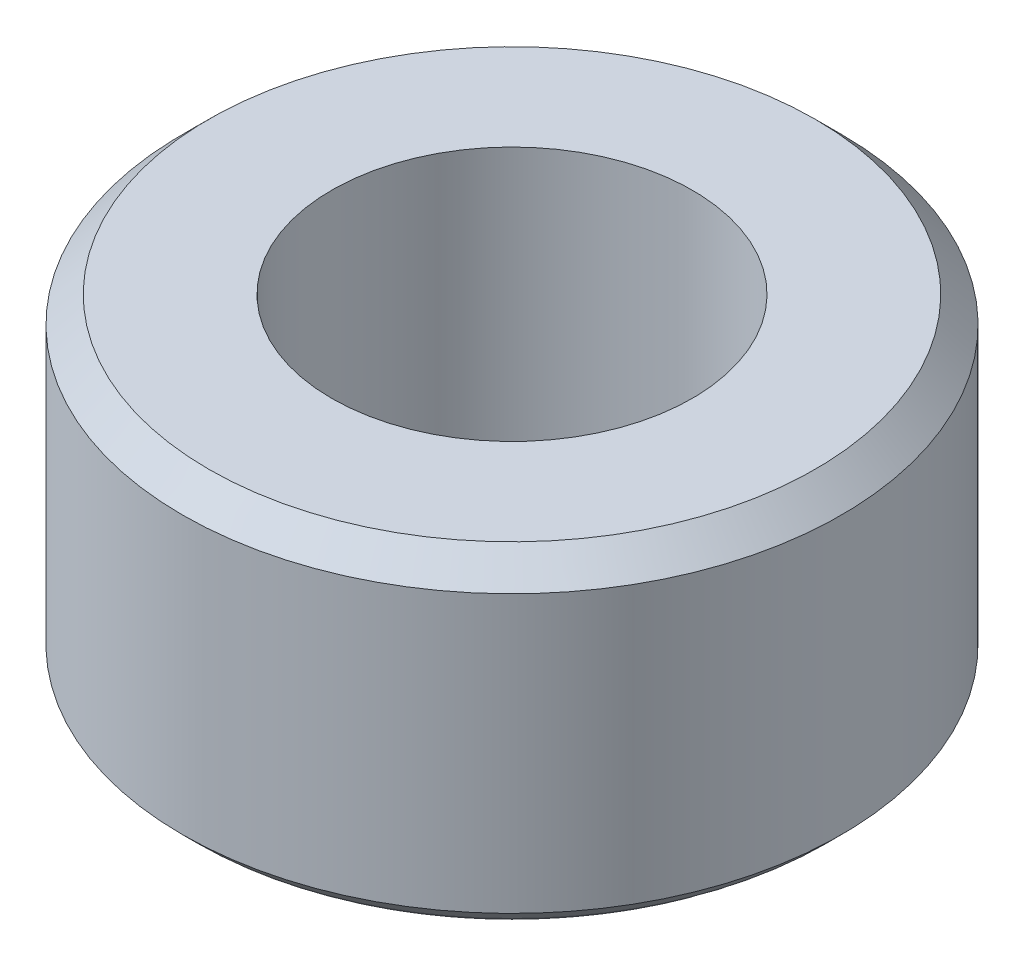
SolidWorks part; units mm, degrees
ref_plane "Front Plane" through (0, 0, 0) normal (0, 0, 1) x (1, 0, 0)
ref_plane "Top Plane" through (0, 0, 0) normal (0, 1, 0) x (1, 0, 0)
ref_plane "Right Plane" through (0, 0, 0) normal (1, 0, 0) x (0, 0, -1)
sketch "Sketch1" plane through (0, 0, 0) normal (0, 1, 0) x (1, 0, 0)
  circle A1 centre (0, 0) radius 6.35
  dimension "D1" = 12.7
extrude "Boss-Extrude1" add sketch "Sketch1" along normal blind 6.35
hole_wizard "1/4 (0.25) Diameter Hole1" positions "Sketch2" profile "Sketch3" hole size "1/4" standard "ANSI Inch" end condition through all
sketch "Sketch2" plane through (0, 6.35, 0) normal (0, 1, 0) x (1, 0, 0)
  point P0 (0, 0)
sketch "Sketch3" plane through (0, 6.35, 0) normal (1, 0, 0) x (0, 0, 1)
  line L0 (0, 0) -> (0, 6.35)
  line L1 (0, 6.35) -> (3.475, 6.35)
  line L2 (3.475, 6.35) -> (3.475, 0)
  line L5 (3.475, 0) -> (0, 0)
  line L11 (0, -6.35) -> (0, 107.95) construction
  dimension "Thru Hole Dia." = 6.95
  dimension "Thru Hole Depth" = 6.35
chamfer "Chamfer1" distance 0.508 angle 45 2 edges at (0, 0, 6.35) (0, 6.35, 6.35)
fillet "Fillet1" radius 0.76 1 edges at (0, 0, 5.842)
